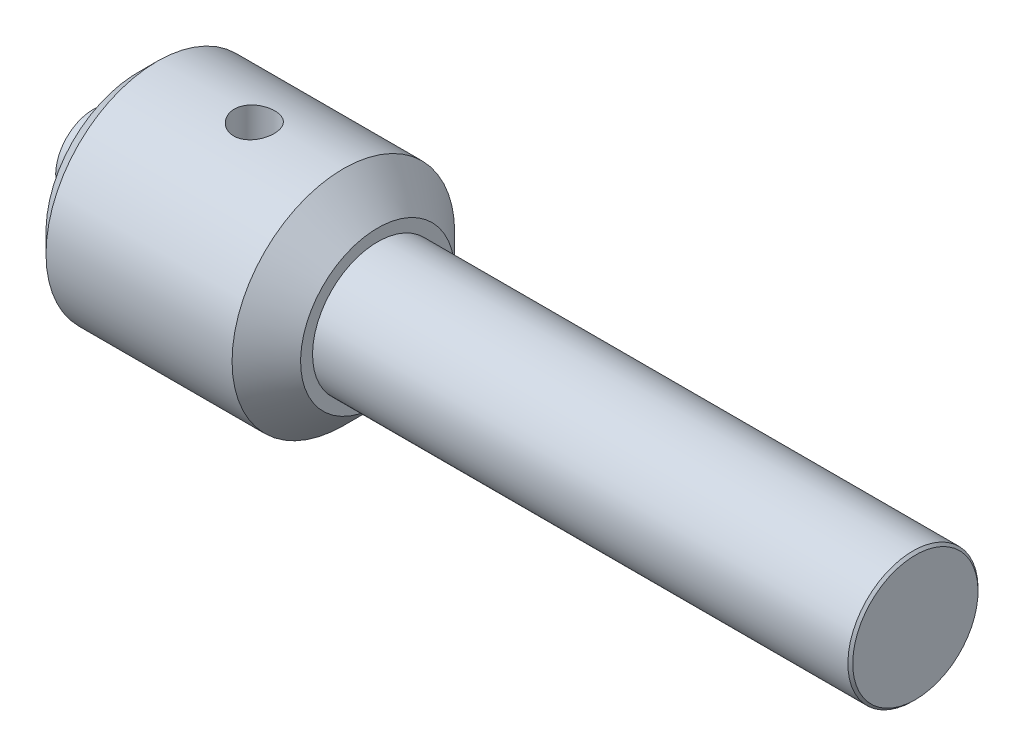
SolidWorks part; units mm, degrees
ref_plane "Front Plane" through (0, 0, 0) normal (0, 0, 1) x (1, 0, 0)
ref_plane "Top Plane" through (0, 0, 0) normal (0, 1, 0) x (1, 0, 0)
ref_plane "Right Plane" through (0, 0, 0) normal (1, 0, 0) x (0, 0, -1)
sketch "Sketch1" plane through (0, 0, 0) normal (0, 0, 1) x (1, 0, 0)
  line L0 (-169.5941, 0) -> (119.9467, 0) construction
  line L1 (70.4059, 0) -> (70.4059, 18.2929)
  line L2 (70.4059, 18.2929) -> (69.6988, 19)
  line L3 (69.6988, 19) -> (-86.5941, 19)
  line L4 (-86.5941, 19) -> (-86.5941, 22.5)
  line L5 (-86.5941, 22.5) -> (-96.5941, 32.5)
  line L6 (-96.5941, 32.5) -> (-150.921, 32.5)
  line L7 (-150.921, 32.5) -> (-156.5941, 26.8268)
  line L8 (-156.5941, 26.8268) -> (-156.5941, 11)
  line L9 (-156.5941, 11) -> (-169.5941, 11)
  line L10 (-169.5941, 11) -> (-169.5941, 0)
  line L11 (69.6988, 19) -> (82.3392, 19) construction
  line L12 (-96.5941, 32.5) -> (-76.8497, 32.5) construction
  line L15 (-169.5941, 0) -> (70.4059, 0)
  dimension "D1" = 45
  dimension "D2" = 1
  dimension "D3" = 32.5
  dimension "19" = 19
  dimension "D4" = 11
  dimension "D5" = 13
  dimension "D6" = 10
  dimension "D7" = 240
  dimension "D8" = 45
  dimension "D9" = 32.5
  dimension "D10" = 8.0231
  dimension "D11" = 83
revolve "Revolve2" add sketch "Sketch1" angle 360 about L15
cosmetic thread "Cosmetic Thread1" parameters "D2"=37
sketch "Sketch2" plane through (0, 0, 0) normal (0, 1, 0) x (1, 0, 0)
  line L1 (-86.5941, -22.5) -> (-86.5941, 22.5) construction
  circle A0 centre (-121.5941, -1.0089) radius 6
  dimension "D2" = 12
  dimension "D1" = 35
extrude "Cut-Extrude1" cut sketch "Sketch2" against normal through all both and the other way through all contours A0
sketch "Sketch3" plane through (-169.5941, 0, 0) normal (-1, 0, 0) x (0, 0, 1)
  circle A0 centre (0, 0) radius 6
  dimension "D1" = 12
extrude "Cut-Extrude2" cut sketch "Sketch3" against normal blind 30
sketch "Sketch4" plane through (70.4059, 0, 0) normal (1, 0, 0) x (0, 0, -1)
  circle A0 centre (0, 0) radius 5.5
  dimension "D1" = 11
sketch "Sketch5" plane through (-139.5941, 0, 0) normal (-1, 0, 0) x (0, 0, 1)
  circle A0 centre (0, 0) radius 5.5
extrude "Cut-Extrude4" cut sketch "Sketch5" against normal blind 5
